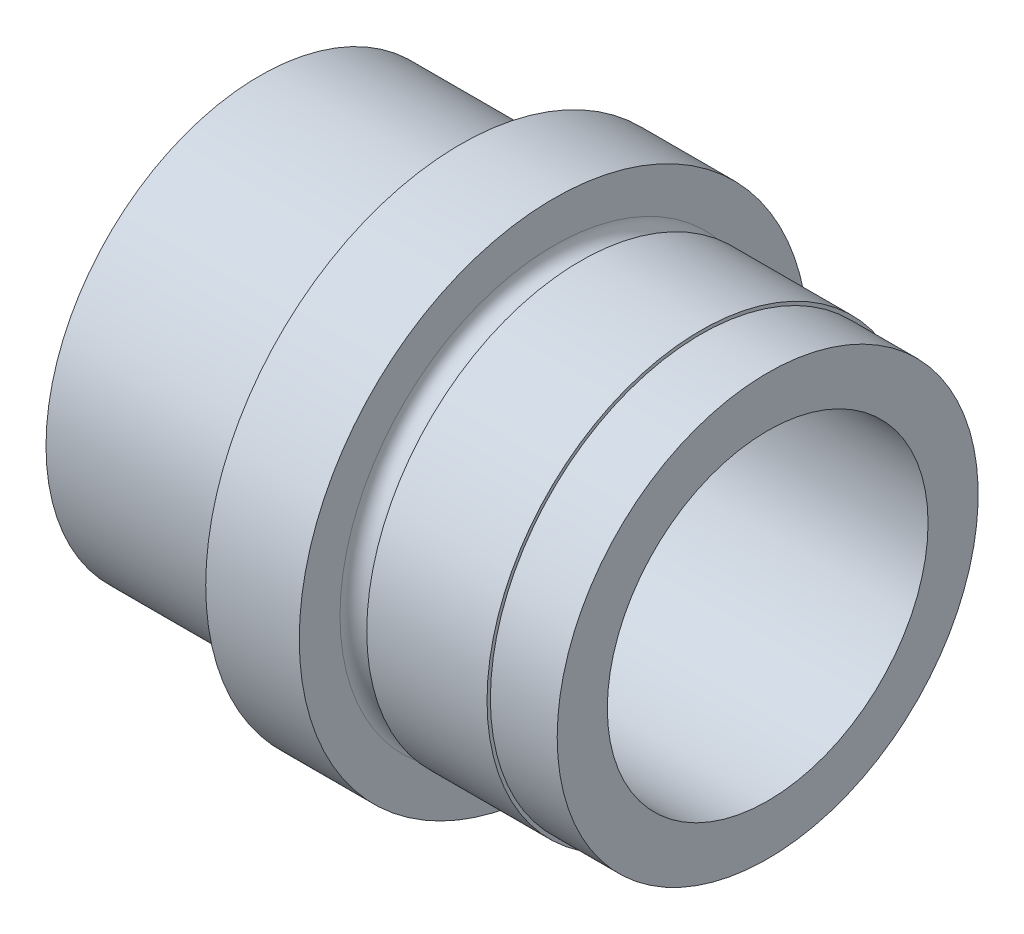
SolidWorks part; units mm, degrees
ref_plane "Plano frontal" through (0, 0, 0) normal (0, 0, 1) x (1, 0, 0)
ref_plane "Plano superior" through (0, 0, 0) normal (0, 1, 0) x (1, 0, 0)
ref_plane "Plano direito" through (0, 0, 0) normal (1, 0, 0) x (0, 0, -1)
sketch "Esboço1" plane through (0, 0, 0) normal (0, 0, 1) x (1, 0, 0)
  line L0 (-90.6162, 0) -> (90.6162, 0) construction
  line L1 (0, 12.25) -> (0, 16)
  line L2 (0, 16) -> (13, 16)
  line L3 (15, 16) -> (15, 19.05)
  line L4 (15, 19.05) -> (22, 19.05)
  line L5 (22, 19.05) -> (22, 16)
  line L6 (24, 16) -> (33, 16)
  line L7 (38, 15.75) -> (38, 12)
  line L8 (38, 12) -> (5, 12)
  line L9 (5, 12) -> (5, 12.25)
  line L10 (5, 12.25) -> (0, 12.25)
  line L11 (33, 16) -> (33, 15.75)
  line L12 (33, 15.75) -> (38, 15.75)
  line L13 (0, 12.25) -> (0, 0) construction
  arc A0 (13, 16) -> (15, 16) centre (14, 16) ccw
  arc A1 (22, 16) -> (24, 16) centre (23, 16) ccw
  dimension "D9" = 1
  dimension "D1" = 24
  dimension "D2" = 32
  dimension "D3" = 31.5
  dimension "D4" = 5
  dimension "D5" = 24.5
  dimension "D6" = 5
  dimension "D7" = 7
  dimension "D8" = 16
  dimension "D10" = 38
  dimension "D11" = 38.1
revolve "Revolução1" add sketch "Esboço1" angle 360 about L0
